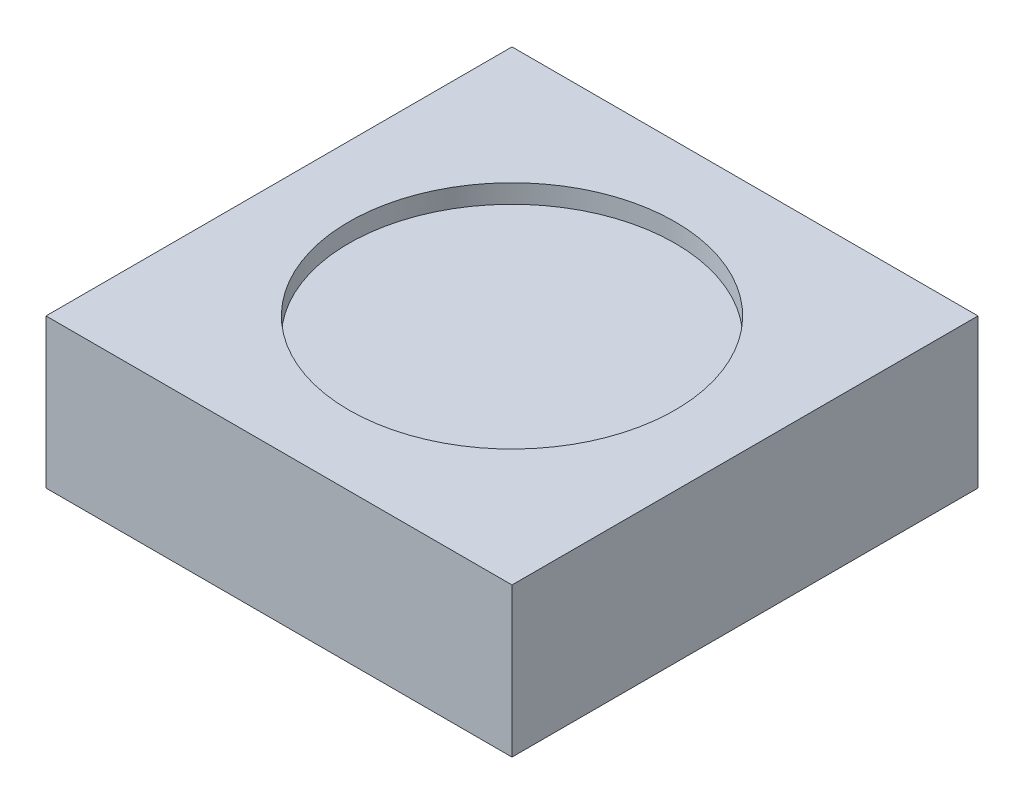
SolidWorks part; units mm, degrees
ref_plane "Front Plane" through (0, 0, 0) normal (0, 0, 1) x (1, 0, 0)
ref_plane "Top Plane" through (0, 0, 0) normal (0, 1, 0) x (1, 0, 0)
ref_plane "Right Plane" through (0, 0, 0) normal (1, 0, 0) x (0, 0, -1)
sketch "Sketch1" plane through (0, 0, 0) normal (0, 1, 0) x (1, 0, 0)
  line L1 (-2.5, -2.5) -> (2.5, -2.5)
  line L2 (-2.5, -2.5) -> (-2.5, 2.5)
  line L3 (-2.5, 2.5) -> (2.5, 2.5)
  line L4 (2.5, -2.5) -> (2.5, 2.5)
  line L5 (-2.5, -2.5) -> (2.5, 2.5) construction
  line L6 (-2.5, 2.5) -> (2.5, -2.5) construction
  point P0 (0, 0)
  dimension "D1" = 5
  dimension "D2" = 5
extrude "Boss-Extrude1" add sketch "Sketch1" along normal blind 1.6
sketch "Sketch2" plane through (0, 1.6, 0) normal (0, 1, 0) x (1, 0, 0)
  circle A0 centre (0, 0) radius 1.75
  dimension "D1" = 3.5
extrude "Cut-Extrude1" cut sketch "Sketch2" against normal blind 0.2
